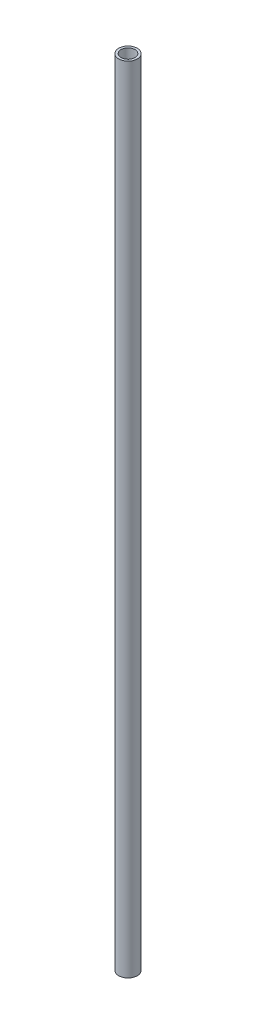
SolidWorks part; units mm, degrees
material "Copper"
ref_plane "Front Plane" through (0, 0, 0) normal (0, 0, 1) x (1, 0, 0)
ref_plane "Top Plane" through (0, 0, 0) normal (0, 1, 0) x (1, 0, 0)
ref_plane "Right Plane" through (0, 0, 0) normal (1, 0, 0) x (0, 0, -1)
sketch "Sketch1" plane through (0, 0, 0) normal (0, 1, 0) x (1, 0, 0)
  circle A0 centre (0, 0) radius 2
  circle A1 centre (0, 0) radius 1.5
  dimension "D1" = 4
  dimension "D2" = 3
extrude "Boss-Extrude1" add sketch "Sketch1" along normal mid plane 171
